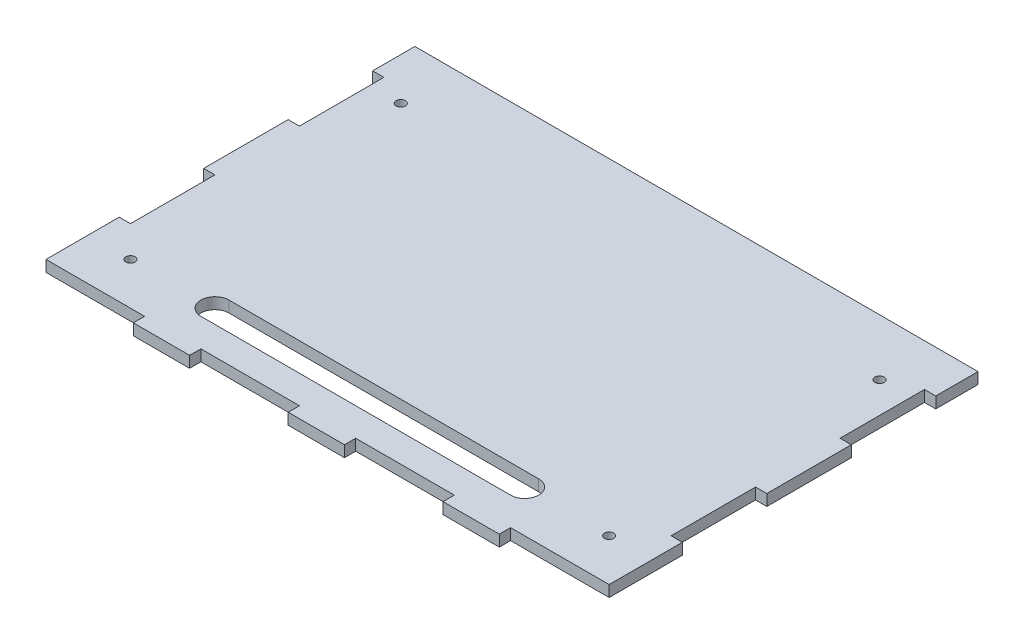
SolidWorks part; units mm, degrees
ref_plane "Plano frontal" through (0, 0, 0) normal (0, 0, 1) x (1, 0, 0)
ref_plane "Plano superior" through (0, 0, 0) normal (0, 1, 0) x (1, 0, 0)
ref_plane "Plano direito" through (0, 0, 0) normal (1, 0, 0) x (0, 0, -1)
sketch "Esboço1" plane through (0, 0, 0) normal (0, 1, 0) x (1, 0, 0)
  line L0 (-100, 75) -> (100, -75) construction
  line L1 (-100, 75) -> (100, 75)
  line L2 (-100, 75) -> (-100, -75)
  line L3 (-100, -75) -> (100, -75)
  line L4 (100, 75) -> (100, -75)
  point P4 (0, 0)
  dimension "D1" = 200
  dimension "D2" = 150
extrude "Ressalto-extrusão1" add sketch "Esboço1" along normal blind 4
sketch "Esboço2" plane through (0, 4, 0) normal (0, 1, 0) x (1, 0, 0)
  line L0 (-65, -75) -> (-65, -71)
  line L1 (-100, -75) -> (100, -75) construction
  line L2 (-65, -71) -> (-45, -71)
  line L3 (-45, -71) -> (-45, -75)
  line L4 (-45, -75) -> (-10, -75)
  line L5 (-10, -75) -> (-10, -71)
  line L6 (-10, -71) -> (10, -71)
  line L7 (10, -71) -> (10, -75)
  line L8 (10, -75) -> (45, -75)
  line L9 (45, -75) -> (45, -71)
  line L10 (45, -71) -> (65, -71)
  line L11 (65, -71) -> (65, -75)
  line L12 (-100, 75) -> (-100, -75) construction
  line L13 (0, 0) -> (0, 75) construction
  line L15 (10, -71) -> (45, -71)
  line L17 (-65, -75) -> (-100, -75)
  line L18 (-100, -75) -> (-100, -71)
  line L19 (-100, -71) -> (-65, -71)
  line L20 (-45, -71) -> (-10, -71)
  line L21 (65, -71) -> (100, -71)
  line L22 (100, -75) -> (100, 75) construction
  line L23 (100, -45) -> (96, -45)
  line L24 (96, -45) -> (96, -15)
  line L25 (96, -15) -> (100, -15)
  line L26 (100, -15) -> (100, 15)
  line L27 (100, 15) -> (96, 15)
  line L28 (96, 15) -> (96, 45)
  line L29 (96, 45) -> (100, 45)
  line L30 (100, 75) -> (-100, 75) construction
  line L31 (-100, -15) -> (-100, -45)
  line L32 (-100, 45) -> (-100, 15)
  line L33 (-96, 45) -> (-100, 45)
  line L34 (100, 45) -> (100, 15)
  line L35 (100, -15) -> (100, -45)
  line L36 (-96, 15) -> (-96, 45)
  line L37 (-100, 15) -> (-96, 15)
  line L38 (-100, -15) -> (-100, 15)
  line L39 (-96, -15) -> (-100, -15)
  line L40 (-96, -45) -> (-96, -15)
  line L41 (-100, -45) -> (-96, -45)
  line M8 (-100, 75) -> (-100, -75)
  line M9 (-100, -75) -> (100, -75)
  line M10 (100, -75) -> (100, 75)
  dimension "D1" = 35
  dimension "D2" = 35
  dimension "D3" = 35
  dimension "D4" = 20
  dimension "D5" = 20
  dimension "D6" = 20
  dimension "D7" = 4
  dimension "D8" = 30
  dimension "D9" = 30
  dimension "D10" = 30
  dimension "D11" = 30
  dimension "D12" = 4
extrude "Corte-extrusão1" cut sketch "Esboço2" against normal through all contours L20 L3 L5 M9 | L15 L7 L9 M9 | L21 L11 M9 M10 | L19 L0 M8 M9 | L27 L28 L29 L34 | L35 L23 L24 L25 | L37 L36 L33 L32 | L31 L41 L40 L39
sketch "Esboço3" plane through (0, 4, 0) normal (0, 1, 0) x (1, 0, 0)
  line L0 (100, 45) -> (100, 75) construction
  line L1 (-100, 75) -> (100, 75)
  line L2 (-100, 75) -> (-100, 60)
  line L3 (-100, 60) -> (100, 60)
  line L4 (100, 75) -> (100, 60)
  dimension "D1" = 15
extrude "Corte-extrusão2" cut sketch "Esboço3" against normal through all
hole_wizard "Broca de rosquear para tarraxa de M41" positions "3DSketch1" profile "Esboço4" hole size "M4" standard "ISO" end condition through all
sketch3d "3DSketch1"
  line L0 (-100, 4, -60) -> (-100, 4, -45) construction
  line L1 (-100, 4, -60) -> (100, 4, -60) construction
  line L2 (-100, 4, 45) -> (-100, 4, 71) construction
  line L3 (-100, 4, 71) -> (-65, 4, 71) construction
  line L4 (100, 4, 71) -> (100, 4, 45) construction
  line L5 (65, 4, 71) -> (100, 4, 71) construction
  line L6 (100, 4, -45) -> (100, 4, -60) construction
  point P0 (-85, 4, -40)
  point P2 (-85, 4, 56)
  point P4 (85, 4, 56)
  point P6 (85, 4, -40)
  dimension "D1" = 15
  dimension "D2" = 20
  dimension "D3" = 15
  dimension "D4" = 15
  dimension "D5" = 15
  dimension "D6" = 15
  dimension "D7" = 15
  dimension "D8" = 20
sketch "Esboço4" plane through (-85, 4, -40) normal (1, 0, 0) x (0, 0, 1)
  line L0 (0, 0) -> (0, 4)
  line L1 (0, 4) -> (1.65, 4)
  line L2 (1.65, 4) -> (1.65, 0)
  line L5 (1.65, 0) -> (0, 0)
  line L11 (0, -6.35) -> (0, 107.95) construction
  dimension "Thru Hole Dia." = 3.3
  dimension "Thru Hole Depth" = 4
sketch "Esboço5" plane through (0, 4, 0) normal (0, 1, 0) x (1, 0, 0)
  line L0 (55, -56) -> (-55, -56) construction
  line L1 (55, -61) -> (-55, -61)
  line L2 (55, -51) -> (-55, -51)
  line L3 (-85, -56) -> (83.35, -56) construction
  line L4 (0, 60) -> (0, -75) construction
  arc A0 (55, -61) -> (55, -51) centre (55, -56) ccw
  arc A1 (-55, -51) -> (-55, -61) centre (-55, -56) ccw
  circle A5 centre (-85, -56) radius 1.65
  circle A6 centre (-85, -56) radius 1.65 construction
  point P2 (0, -56)
  dimension "D2" = 5
  dimension "D1" = 110
extrude "Corte-extrusão3" cut sketch "Esboço5" against normal through all
